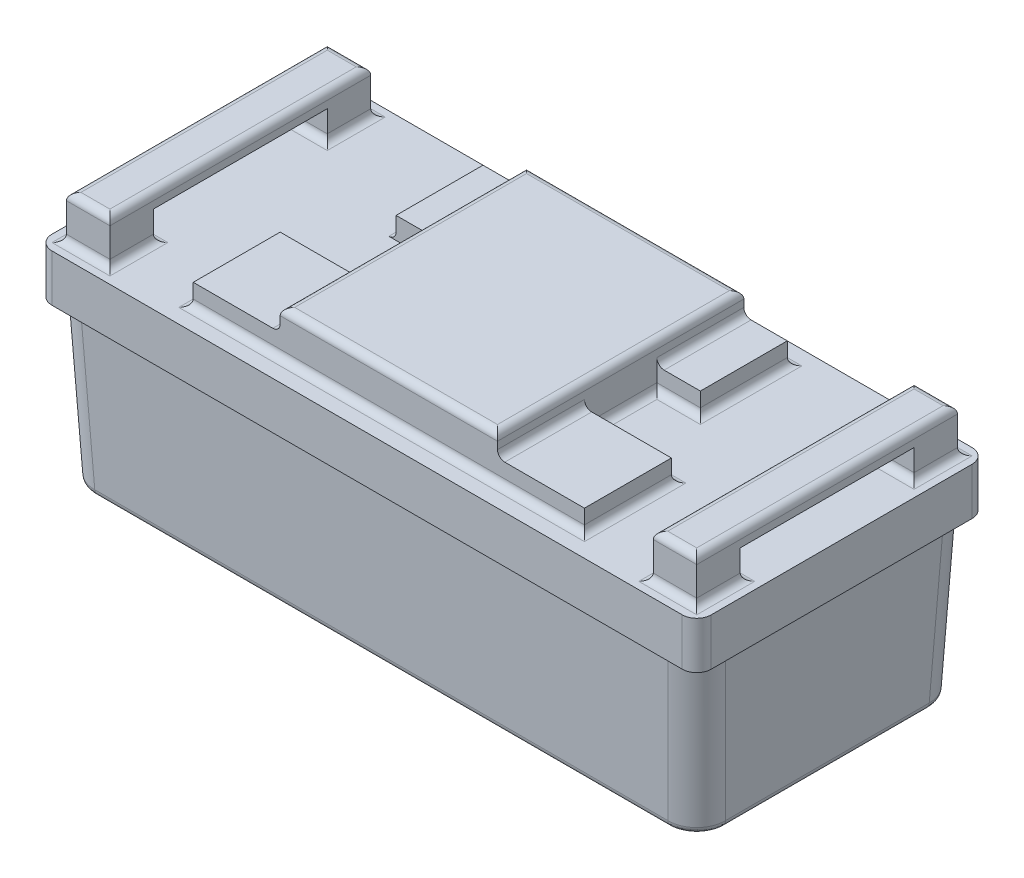
SolidWorks part; units mm, degrees
ref_plane "Front Plane" through (0, 0, 0) normal (0, 0, 1) x (1, 0, 0)
ref_plane "Top Plane" through (0, 0, 0) normal (0, 1, 0) x (1, 0, 0)
ref_plane "Right Plane" through (0, 0, 0) normal (1, 0, 0) x (0, 0, -1)
sketch "Sketch1" plane through (0, 0, 0) normal (0, 1, 0) x (1, 0, 0)
  line L1 (-288.925, -127) -> (288.925, -127)
  line L2 (-288.925, -127) -> (-288.925, 127)
  line L3 (-288.925, 127) -> (288.925, 127)
  line L4 (288.925, -127) -> (288.925, 127)
  line L5 (-288.925, -127) -> (288.925, 127) construction
  line L6 (-288.925, 127) -> (288.925, -127) construction
  point P0 (0, 0)
  dimension "D1" = 577.85
  dimension "D2" = 254
extrude "Boss-Extrude1" add sketch "Sketch1" along normal blind 41.275
sketch "Sketch2" plane through (0, 41.275, 0) normal (0, 1, 0) x (1, 0, 0)
  line L0 (-288.925, 127) -> (-288.925, -127) construction
  line L1 (-276.225, 114.3) -> (-238.125, 114.3)
  line L2 (-276.225, 114.3) -> (-276.225, -114.3)
  line L3 (-276.225, -114.3) -> (-238.125, -114.3)
  line L4 (-238.125, 114.3) -> (-238.125, -114.3)
  line L5 (238.125, 114.3) -> (276.225, 114.3)
  line L6 (238.125, 114.3) -> (238.125, -114.3)
  line L7 (238.125, -114.3) -> (276.225, -114.3)
  line L8 (276.225, 114.3) -> (276.225, -114.3)
  line L9 (288.925, -127) -> (288.925, 127) construction
  point P8 (-276.225, 0)
  point P9 (-238.125, 0)
  point P11 (238.125, 0)
  point P12 (276.225, 0)
  dimension "D1" = 38.1
  dimension "D2" = 38.1
  dimension "D3" = 228.6
  dimension "D4" = 228.6
  dimension "D5" = 12.7
  dimension "D6" = 12.7
extrude "Boss-Extrude2" add sketch "Sketch2" along normal blind 38.1
sketch "Sketch3" plane through (-276.225, 0, 0) normal (-1, 0, 0) x (0, 0, 1)
  line L0 (-127, 41.275) -> (127, 41.275) construction
  line L1 (-76.2, 41.275) -> (76.2, 41.275)
  line L2 (-76.2, 41.275) -> (-76.2, 66.675)
  line L3 (-76.2, 66.675) -> (76.2, 66.675)
  line L4 (76.2, 41.275) -> (76.2, 66.675)
  line L5 (-114.3, 79.375) -> (-114.3, 41.275) construction
  line L6 (114.3, 79.375) -> (114.3, 41.275) construction
  point P8 (-114.3, 60.325)
  dimension "D1" = 25.4
  dimension "D2" = 38.1
  dimension "D3" = 38.1
extrude "Cut-Extrude1" cut sketch "Sketch3" against normal up to surface (552.45 mm away) up to face at (276.225, 60.325, 0)
sketch "Sketch4" plane through (0, 41.275, 0) normal (0, 1, 0) x (1, 0, 0)
  line L1 (-171.45, -107.95) -> (171.45, -107.95)
  line L2 (-171.45, -107.95) -> (-171.45, 107.95)
  line L3 (-171.45, 107.95) -> (171.45, 107.95)
  line L4 (171.45, -107.95) -> (171.45, 107.95)
  line L5 (-171.45, -107.95) -> (171.45, 107.95) construction
  line L6 (-171.45, 107.95) -> (171.45, -107.95) construction
  point P0 (0, 0)
  dimension "D1" = 215.9
  dimension "D2" = 342.9
extrude "Boss-Extrude3" add sketch "Sketch4" along normal blind 38.1
sketch "Sketch6" plane through (0, 79.375, 0) normal (0, 1, 0) x (1, 0, 0)
  line L0 (-171.45, -31.75) -> (-95.25, -31.75)
  line L1 (-171.45, 107.95) -> (-171.45, -107.95) construction
  line L2 (-95.25, -31.75) -> (-95.25, 31.75)
  line L3 (-95.25, 31.75) -> (-133.35, 31.75)
  line L4 (-133.35, 31.75) -> (-133.35, 107.95)
  line L5 (171.45, 107.95) -> (-171.45, 107.95) construction
  line L6 (-133.35, 107.95) -> (-171.45, 107.95)
  line L7 (-171.45, 107.95) -> (-171.45, -31.75)
  line L8 (95.25, -31.75) -> (171.45, -31.75)
  line L9 (171.45, -107.95) -> (171.45, 107.95) construction
  line L10 (171.45, -31.75) -> (171.45, 107.95)
  line L11 (171.45, 107.95) -> (133.35, 107.95)
  line L12 (171.45, 107.95) -> (-171.45, 107.95) construction
  line L13 (133.35, 107.95) -> (133.35, 31.75)
  line L14 (133.35, 31.75) -> (95.25, 31.75)
  line L15 (95.25, 31.75) -> (95.25, -31.75)
  line L16 (-171.45, -107.95) -> (171.45, -107.95) construction
  point P24 (-133.35, -31.75)
  dimension "D1" = 76.2
  dimension "D2" = 63.5
  dimension "D3" = 76.2
  dimension "D4" = 76.2
  dimension "D5" = 38.1
  dimension "D6" = 38.1
extrude "Cut-Extrude2" cut sketch "Sketch6" against normal up to surface (38.1 mm away) up to face at (-257.175, 41.275, -95.25)
sketch "Sketch7" plane through (0, 79.375, 0) normal (0, 1, 0) x (1, 0, 0)
  line L0 (-171.45, -107.95) -> (171.45, -107.95) construction
  line L1 (-171.45, -31.75) -> (-95.25, -31.75)
  line L2 (-171.45, -31.75) -> (-171.45, -107.95)
  line L3 (-171.45, -107.95) -> (-95.25, -107.95)
  line L4 (-95.25, -31.75) -> (-95.25, -107.95)
  line L6 (-95.25, 31.75) -> (-133.35, 31.75)
  line L7 (-95.25, 31.75) -> (-95.25, 107.95)
  line L8 (-95.25, 107.95) -> (-133.35, 107.95)
  line L9 (-133.35, 31.75) -> (-133.35, 107.95)
  line L10 (95.25, 31.75) -> (133.35, 31.75)
  line L11 (95.25, 31.75) -> (95.25, 107.95)
  line L12 (95.25, 107.95) -> (133.35, 107.95)
  line L13 (133.35, 31.75) -> (133.35, 107.95)
  line L14 (95.25, -31.75) -> (171.45, -31.75)
  line L15 (95.25, -31.75) -> (95.25, -107.95)
  line L16 (95.25, -107.95) -> (171.45, -107.95)
  line L17 (171.45, -31.75) -> (171.45, -107.95)
extrude "Cut-Extrude3" cut sketch "Sketch7" against normal blind 19.05
fillet "Fillet1" radius 6.35 36 edges at (95.25, 79.375, 0) (133.35, 41.275, 31.75) (133.35, 41.275, -69.85) (95.25, 41.275, 0) (-95.25, 60.325, 69.85) (-95.25, 60.325, -69.85) (95.25, 60.325, -69.85) (95.25, 60.325, 69.85) (-276.225, 41.275, -95.25) (-238.125, 41.275, 95.25) (-276.225, 79.375, 0) (-257.175, 79.375, 114.3) (-238.125, 79.375, 0) (-257.175, 79.375, -114.3) (238.125, 41.275, -95.25) (276.225, 41.275, 95.25) (238.125, 79.375, 0) (257.175, 79.375, 114.3) (276.225, 79.375, 0) (257.175, 79.375, -114.3) (276.225, 41.275, -95.25) (238.125, 41.275, 95.25) (-238.125, 41.275, -95.25) (-276.225, 41.275, 95.25) (-257.175, 41.275, -76.2) (257.175, 41.275, -76.2) (-257.175, 41.275, 76.2) (257.175, 41.275, 76.2) (171.45, 41.275, 69.85) (0, 41.275, 107.95) (-171.45, 41.275, 69.85) (-95.25, 79.375, 0) (-133.35, 41.275, 31.75) (-95.25, 41.275, 0) (-133.35, 41.275, -69.85) (0, 41.275, -107.95)
fillet "Fillet2" radius 12.7 4 edges at (288.925, 20.6375, 127) (288.925, 20.6375, -127) (-288.925, 20.6375, 127) (-288.925, 20.6375, -127)
sketch "Sketch8" plane through (0, 0, 0) normal (0, -1, 0) x (1, 0, 0)
  line L0 (-288.925, -114.3) -> (-288.925, 114.3) construction
  line L1 (-282.575, -120.65) -> (282.575, -120.65)
  line L2 (-282.575, -120.65) -> (-282.575, 120.65)
  line L3 (-282.575, 120.65) -> (282.575, 120.65)
  line L4 (282.575, -120.65) -> (282.575, 120.65)
  line L5 (-282.575, -120.65) -> (282.575, 120.65) construction
  line L6 (-282.575, 120.65) -> (282.575, -120.65) construction
  line L7 (-276.225, 127) -> (276.225, 127) construction
  point P0 (0, 0)
  dimension "D1" = 6.35
  dimension "D2" = 6.35
ref_plane "Plane1" through (0, -139.7, 0) normal (0, -1, 0) x (-1, 0, 0)
sketch "Sketch9" plane through (0, -139.7, 0) normal (0, -1, 0) x (-1, 0, 0)
  line L8 (276.225, 114.3) -> (-276.225, 114.3)
  line L9 (276.225, -114.3) -> (276.225, 114.3)
  line L10 (-276.225, -114.3) -> (276.225, -114.3)
  line L11 (-276.225, 114.3) -> (-276.225, -114.3)
  line L12 (276.225, 114.3) -> (-276.225, 114.3)
  line L13 (276.225, -114.3) -> (276.225, 114.3)
  line L14 (-276.225, -114.3) -> (276.225, -114.3)
  line L15 (-276.225, 114.3) -> (-276.225, -114.3)
  dimension "D1" = 6.35
loft "Loft1" add profiles "Sketch8", "Sketch9"
fillet "Fillet3" radius 25.4 4 edges
fillet "Fillet4" radius 6.35 8 edges
